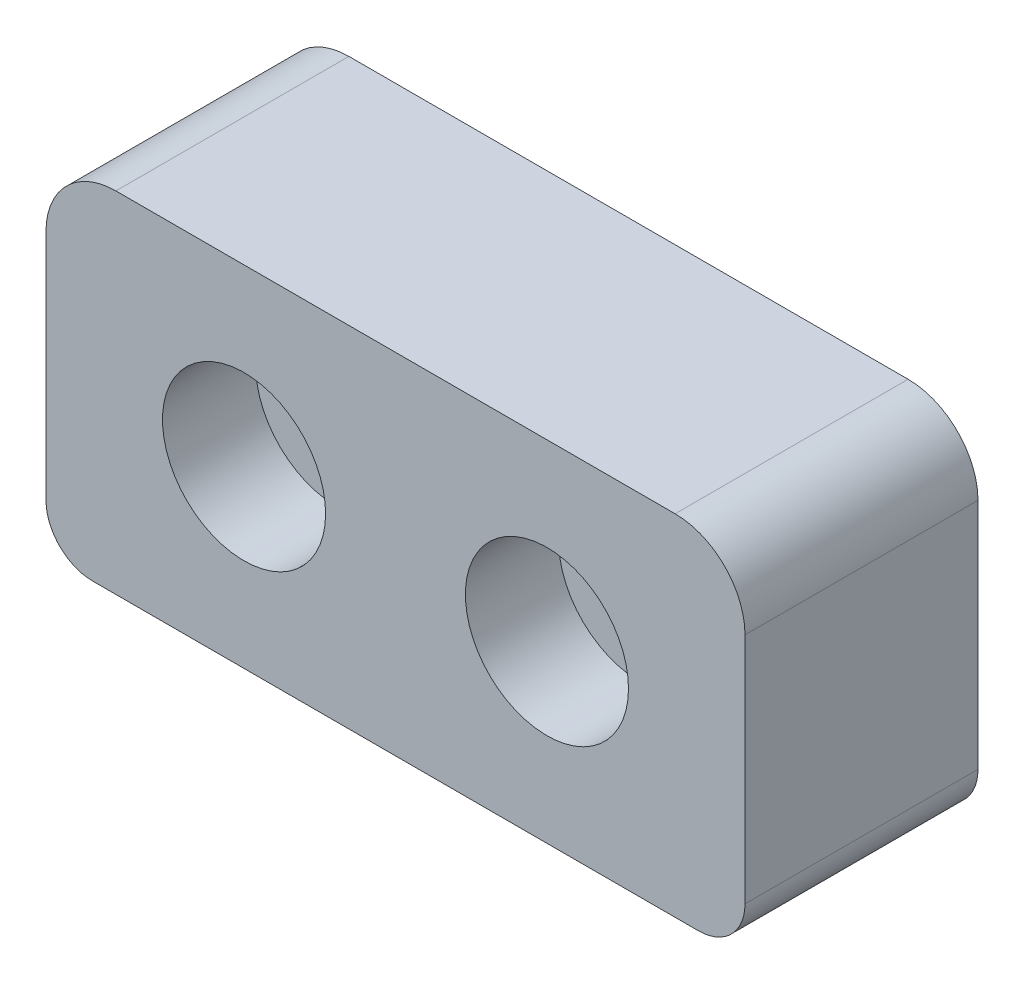
SolidWorks part; units mm, degrees
material "ABS"
ref_plane "前视基准面" through (0, 0, 0) normal (0, 0, 1) x (1, 0, 0)
ref_plane "上视基准面" through (0, 0, 0) normal (0, 1, 0) x (1, 0, 0)
ref_plane "右视基准面" through (0, 0, 0) normal (1, 0, 0) x (0, 0, -1)
other "Configuration Table"
sketch "草图1" plane through (0, 0, 0) normal (0, 0, 1) x (1, 0, 0)
  line L0 (7.25, 0) -> (-7.25, 0)
  line L1 (-7.25, 0) -> (-7.25, 5)
  line L2 (-7.25, 5) -> (-15, 5)
  line L3 (-15, 5) -> (-15, -15)
  line L4 (0, 0) -> (0, -15) construction
  line L5 (15, -15) -> (-15, -15)
  line L6 (15, 5) -> (15, -15)
  line L7 (7.25, 5) -> (15, 5)
  line L8 (7.25, 0) -> (7.25, 5)
  dimension "D1" = 14.5
  dimension "D2" = 5
  dimension "D3" = 30
  dimension "D4" = 15
extrude "凸台-拉伸1" add sketch "草图1" along normal blind 10
fillet "圆角1" radius 2 4 edges at (-15, -15, 5) (15, -15, 5) (15, 5, 5) (-15, 5, 5)
sketch "草图2" plane through (0, 0, 10) normal (0, 0, 1) x (1, 0, 0)
  line L0 (0, 0) -> (0, 50000) construction
  line L4 (-7.25, 0) -> (-7.25, -15) construction
  line L5 (-13, -15) -> (13, -15) construction
  circle A0 centre (-6.5, -7.5) radius 1.55
  circle A1 centre (6.5, -7.5) radius 1.55
  point P14 (-7.25, -7.5)
  dimension "D1" = 3.1
  dimension "D2" = 13
extrude "切除-拉伸1" cut sketch "草图2" against normal through all
sketch "草图3" plane through (0, 0, 10) normal (0, 0, 1) x (1, 0, 0)
  line L0 (-15, 3) -> (-15, -13) construction
  line L1 (-15, 0) -> (15, 0)
  line L2 (-15, 0) -> (-15, 5)
  line L3 (-15, 5) -> (15, 5)
  line L4 (15, 0) -> (15, 5)
  line L5 (13, 5) -> (7.25, 5) construction
  line L6 (15, -13) -> (15, 3) construction
  line L7 (7.25, 0) -> (-7.25, 0) construction
extrude "切除-拉伸2" cut sketch "草图3" against normal through all both and the other way through all
fillet "圆角2" radius 3 2 edges at (15, 0, 5) (-15, 0, 5)
sketch "草图4" plane through (0, 0, 10) normal (0, 0, 1) x (1, 0, 0)
  circle A0 centre (-6.5, -7.5) radius 3.15
  circle A1 centre (6.5, -7.5) radius 3.15
  dimension "D1" = 6.3
sketch "草图5" plane through (0, 0, 10) normal (0, 0, 1) x (1, 0, 0)
  circle A0 centre (-6.5, -7.5) radius 3.5
  circle A1 centre (6.5, -7.5) radius 3.5
  dimension "D1" = 7
extrude "切除-拉伸3" cut sketch "草图5" against normal blind 4
